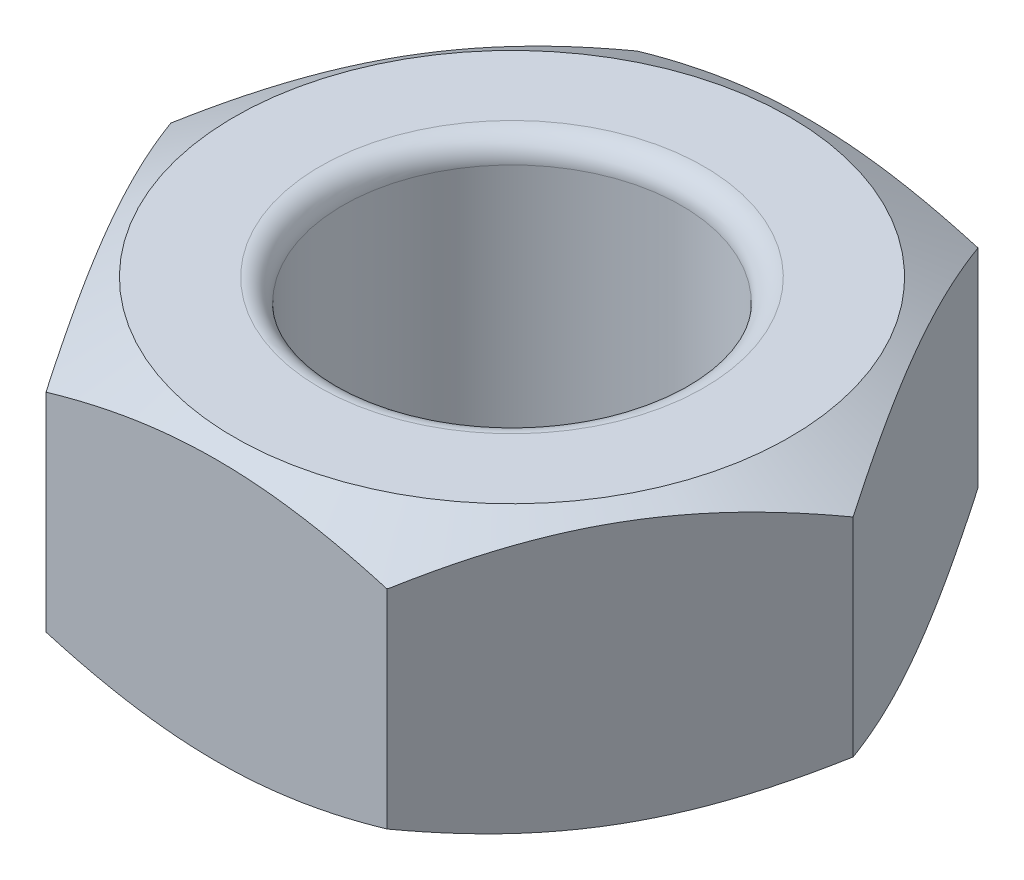
SolidWorks part; units mm, degrees
material "1023 Carbon Steel Sheet (SS)"
ref_plane "Front Plane" through (0, 0, 0) normal (0, 0, 1) x (1, 0, 0)
ref_plane "Top Plane" through (0, 0, 0) normal (0, 1, 0) x (1, 0, 0)
ref_plane "Right Plane" through (0, 0, 0) normal (1, 0, 0) x (0, 0, -1)
sketch "Sketch1" plane through (0, 0, 0) normal (0, 1, 0) x (1, 0, 0)
  line L1 (6.0451, 0) -> (3.0225, 5.2352)
  line L2 (3.0225, 5.2352) -> (-3.0225, 5.2352)
  line L3 (-3.0225, 5.2352) -> (-6.0451, 0)
  line L4 (-6.0451, 0) -> (-3.0225, -5.2352)
  line L5 (-3.0225, -5.2352) -> (3.0225, -5.2352)
  line L6 (3.0225, -5.2352) -> (6.0451, 0)
  circle A0 centre (0, 0) radius 3
  circle A1 centre (0, 0) radius 5.2352 construction
  dimension "D1" = 6
extrude "Boss-Extrude1" add sketch "Sketch1" along normal blind 5
ref_plane "Plane1" through (0, 0, 0) normal (0.866, 0, -0.5) x (-0.5, 0, -0.866)
sketch "Sketch2" plane through (0, 0, 0) normal (0.866, 0, -0.5) x (-0.5, 0, -0.866)
  line L1 (-6.0451, 5) -> (-3.0225, 5) construction
  line L2 (-6.3895, 4.3449) -> (-6.0389, 4.3449)
  line L4 (-6.3895, 4.3449) -> (-6.275, 5.0992)
  line L5 (-6.275, 5.0992) -> (-4.9196, 5)
  line L6 (-6.0389, 4.3449) -> (-4.9196, 5)
  line L7 (0, 0) -> (0, 7.5789) construction
revolve "Cut-Revolve1" cut sketch "Sketch2" angle 360 about L7
ref_plane "Plane2" through (0, 2.5, 0) normal (0, 1, 0) x (1, 0, 0)
mirror "Mirror1" about plane through (0, 2.5, 0) normal (0, 1, 0) of "Cut-Revolve1"
fillet "Fillet1" radius 0.4 2 edges at (0, 0, 3) (0, 5, 3)
